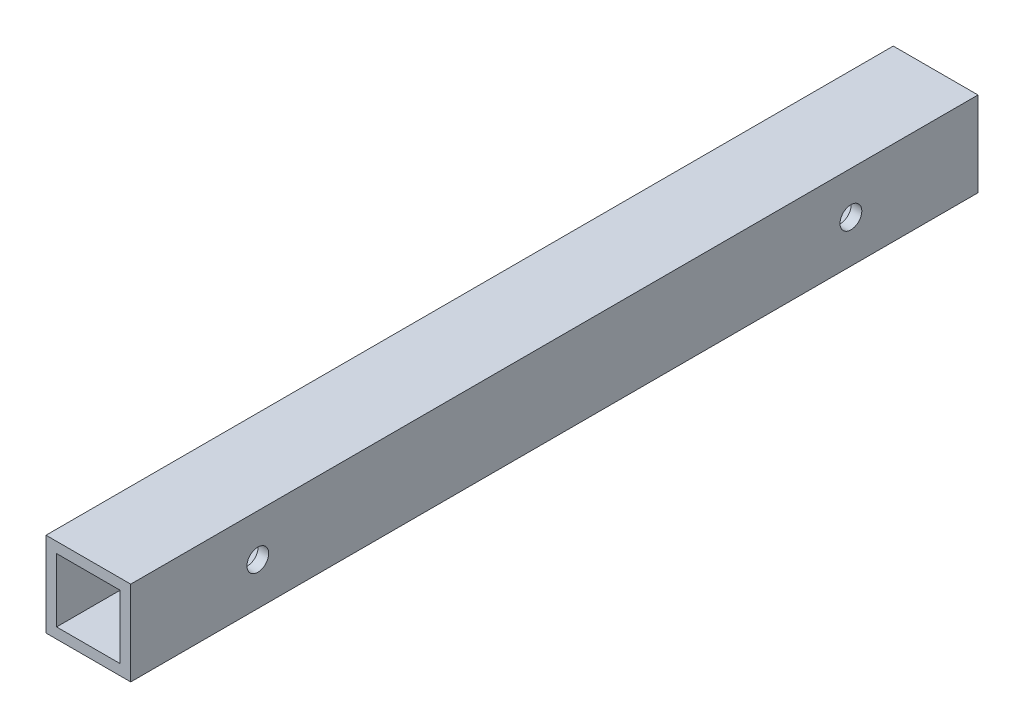
SolidWorks part; units mm, degrees
ref_plane "Front Plane" through (0, 0, 0) normal (0, 0, 1) x (1, 0, 0)
ref_plane "Top Plane" through (0, 0, 0) normal (0, 1, 0) x (1, 0, 0)
ref_plane "Right Plane" through (0, 0, 0) normal (1, 0, 0) x (0, 0, -1)
sketch "Sketch1" plane through (0, 0, 0) normal (0, 0, 1) x (1, 0, 0)
  line L0 (-9.525, 9.525) -> (9.525, 9.525)
  line L1 (-12.7, -12.7) -> (12.7, -12.7)
  line L2 (-12.7, -12.7) -> (-12.7, 12.7)
  line L3 (-12.7, 12.7) -> (12.7, 12.7)
  line L4 (12.7, -12.7) -> (12.7, 12.7)
  line L5 (-12.7, -12.7) -> (12.7, 12.7) construction
  line L6 (-12.7, 12.7) -> (12.7, -12.7) construction
  line L7 (9.525, -9.525) -> (9.525, 9.525)
  line L8 (-9.525, -9.525) -> (9.525, -9.525)
  line L9 (-9.525, -9.525) -> (-9.525, 9.525)
  point P0 (0, 0)
  dimension "D1" = 25.4
  dimension "D2" = 25.4
  dimension "D3" = 3.175
extrude "Boss-Extrude1" add sketch "Sketch1" along normal blind 254
hole_wizard "F (0.257) Diameter Hole1" positions "Sketch2" profile "Sketch3" hole size "F" standard "ANSI Inch" end condition through all
sketch "Sketch2" plane through (12.7, 0, 0) normal (1, 0, 0) x (0, 0, -1)
  line L2 (-254, -12.7) -> (-254, 12.7) construction
  point P2 (-215.9, 0)
  point P6 (-38.1, 0)
  dimension "D1" = 38.1
  dimension "D2" = 38.1
sketch "Sketch3" plane through (12.7, 0, 215.9) normal (0, 1, 0) x (0, 0, -1)
  line L0 (0, 0) -> (0, 25.4)
  line L1 (0, 25.4) -> (3.2639, 25.4)
  line L2 (3.2639, 25.4) -> (3.2639, 0)
  line L5 (3.2639, 0) -> (0, 0)
  line L11 (0, -6.35) -> (0, 107.95) construction
  dimension "Thru Hole Dia." = 6.5278
  dimension "Thru Hole Depth" = 25.4
